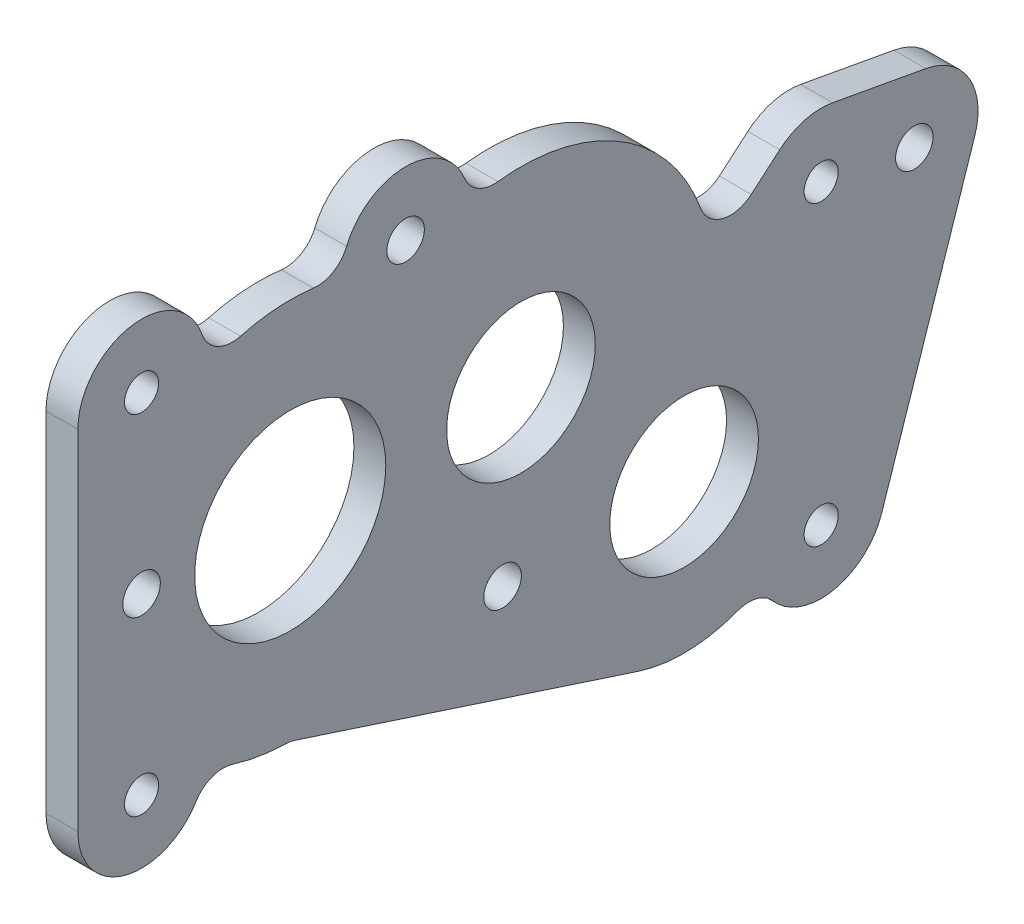
SolidWorks part; units mm, degrees
material "5052-H32"
ref_plane "Front Plane" through (0, 0, 0) normal (0, 0, 1) x (1, 0, 0)
ref_plane "Top Plane" through (0, 0, 0) normal (0, 1, 0) x (1, 0, 0)
ref_plane "Right Plane" through (0, 0, 0) normal (1, 0, 0) x (0, 0, -1)
sketch "Sketch1" plane through (0, 0, 0) normal (1, 0, 0) x (0, 0, -1)
  line L1 (0, 0) -> (146.05, 0)
  line L2 (0, 0) -> (0, 101.6)
  line L3 (0, 101.6) -> (146.05, 101.6)
  line L4 (146.05, 0) -> (146.05, 101.6)
  dimension "D1" = 146.05
  dimension "D2" = 101.6
extrude "Boss-Extrude2" add sketch "Sketch1" along normal blind 4.7625
sketch "Sketch2" plane through (4.7625, 0, 0) normal (1, 0, 0) x (0, 0, -1)
  circle A1 centre (66.2432, 57.15) radius 11.1125
  circle A7 centre (66.2432, 57.15) radius 11.1125
  circle A8 centre (31.75, 57.15) radius 11.1125
  circle A9 centre (31.75, 57.15) radius 11.1125
  circle A10 centre (90.6336, 32.7596) radius 14.2875
  circle A11 centre (90.6336, 32.7596) radius 14.2875
  dimension "D1" = 0
  dimension "D2" = 0
  dimension "D3" = 0
extrude "Cut-Extrude1" cut sketch "Sketch2" against normal through all
hole_wizard "#10 Clearance Hole1" positions "Sketch5" profile "Sketch6" hole size "#10" standard "ANSI Inch" end condition through all
sketch "Sketch5" plane through (4.7625, 0, 0) normal (1, 0, 0) x (0, 0, -1)
  circle A1 centre (111.125, 61.3346) radius 2.5527 construction
  circle A2 centre (9.525, 84.8296) radius 2.5527 construction
  circle A3 centre (9.525, 32.7596) radius 2.5527 construction
  circle A5 centre (111.125, 61.3346) radius 2.5527
  circle A6 centre (9.525, 84.8296) radius 2.5527
  circle A7 centre (9.525, 32.7596) radius 2.5527
  circle A8 centre (111.125, 16.8846) radius 2.5527 construction
  circle A9 centre (111.125, 16.8846) radius 2.5527
  point P423 (9.525, 84.8296)
  point P426 (111.125, 61.3346)
  point P432 (9.525, 32.7596)
  point P469 (111.125, 16.8846)
sketch "Sketch6" plane through (4.7625, 84.8296, -9.525) normal (0, 1, 0) x (0, 0, -1)
  line L0 (0, 0) -> (0, 4.7625)
  line L1 (0, 4.7625) -> (2.5527, 4.7625)
  line L2 (2.5527, 4.7625) -> (2.5527, 0)
  line L5 (2.5527, 0) -> (0, 0)
  line L11 (0, -6.35) -> (0, 107.95) construction
  dimension "Thru Hole Dia." = 5.1054
  dimension "Thru Hole Depth" = 4.7625
hole_wizard "#10 Clearance Hole2" positions "Sketch12" profile "Sketch13" hole size "#10" standard "ANSI Inch" end condition through all
sketch "Sketch12" plane through (4.7625, 0, 0) normal (1, 0, 0) x (0, 0, -1)
  line L0 (48.9966, 84.8296) -> (9.525, 84.8296) construction
  line L1 (9.525, 84.8296) -> (9.525, 32.7596) construction
  line L2 (9.525, 32.7596) -> (63.5, 32.7596) construction
  line L4 (9.525, 58.7946) -> (125.057, 58.7946) construction
  line L5 (66.2432, 57.15) -> (31.75, 57.15) construction
  point P0 (9.525, 58.7946)
  point P2 (48.9966, 84.8296)
  point P4 (125.057, 58.7946)
  point P6 (63.5, 32.7596)
  point P29 (48.9966, 57.15)
  point P30 (0, 0)
  point P31 (0, 0)
  dimension "D1" = 115.532
  dimension "D2" = 53.975
sketch "Sketch13" plane through (4.7625, 58.7946, -9.525) normal (0, 1, 0) x (0, 0, -1)
  line L0 (0, 0) -> (0, 4.7625)
  line L1 (0, 4.7625) -> (2.8067, 4.7625)
  line L2 (2.8067, 4.7625) -> (2.8067, 0)
  line L5 (2.8067, 0) -> (0, 0)
  line L11 (0, -6.35) -> (0, 107.95) construction
  dimension "Thru Hole Dia." = 5.6134
  dimension "Thru Hole Depth" = 4.7625
sketch "Sketch7" plane through (4.7625, 0, 0) normal (1, 0, 0) x (0, 0, -1)
  line L0 (9.525, 32.7596) -> (31.75, 57.15) construction
  line L1 (31.75, 57.15) -> (9.525, 84.8296) construction
  line L2 (31.75, 57.15) -> (66.2432, 57.15) construction
  line L3 (66.2432, 57.15) -> (90.6336, 32.7596) construction
  line L4 (90.6336, 32.7596) -> (111.125, 16.8846) construction
  line L5 (90.6336, 32.7596) -> (111.125, 61.3346) construction
  line L6 (111.125, 61.3346) -> (66.2432, 57.15) construction
  line L7 (94.6948, 59.8027) -> (104.9286, 68.5686)
  line L11 (31.75, 28.575) -> (83.7467, 11.6286)
  line L12 (0, 101.6) -> (146.05, 101.6)
  line L13 (0, 101.6) -> (0, 0)
  line L14 (0, 0) -> (146.05, 0)
  line L15 (146.05, 101.6) -> (146.05, 0)
  line L16 (0, 101.6) -> (0, 0) construction
  line L17 (112.8334, 70.7052) -> (126.7653, 68.1652)
  line L18 (134.0956, 55.7899) -> (120.1637, 13.8799)
  arc A0 (39.4731, 84.6615) -> (18.9777, 31.5883) centre (31.75, 57.15) ccw construction
  arc A1 (48.9966, 79.9334) -> (58.5201, 84.6615) centre (66.2432, 57.15) ccw construction
  arc A2 (103.5854, 50.8207) -> (111.9221, 26.3762) centre (90.6336, 32.7596) ccw construction
  arc A3 (111.9221, 26.3762) -> (120.1637, 13.8799) centre (111.125, 16.8846) ccw construction
  arc A4 (112.8334, 70.7052) -> (105.5742, 53.5942) centre (111.125, 61.3346) ccw construction
  arc A5 (15.9404, 39.8001) -> (18.9777, 31.5883) centre (9.525, 32.7596) ccw construction
  circle A6 centre (9.525, 84.8296) radius 9.525 construction
  arc A7 (104.9286, 68.5686) -> (112.8334, 70.7052) centre (111.125, 61.3346) cw
  arc A9 (120.1637, 13.8799) -> (102.1336, 13.7412) centre (111.125, 16.8846) cw
  arc A12 (31.75, 28.575) -> (18.9777, 31.5883) centre (31.75, 57.15) cw
  arc A13 (18.9777, 31.5883) -> (0, 32.7596) centre (9.525, 32.7596) cw
  arc A15 (0, 84.8296) -> (18.7894, 82.6167) centre (9.525, 84.8296) cw
  arc A16 (18.7894, 82.6167) -> (39.4731, 84.6615) centre (31.75, 57.15) cw
  arc A17 (58.5201, 84.6615) -> (94.6948, 59.8027) centre (66.2432, 57.15) cw
  arc A18 (39.4731, 84.6615) -> (58.5201, 84.6615) centre (48.9966, 84.8296) cw
  circle A19 centre (48.9966, 84.8296) radius 2.8067 construction
  arc A20 (18.9777, 31.5883) -> (48.9966, 79.9334) centre (31.75, 57.15) ccw construction
  arc A21 (83.7467, 11.6286) -> (102.1965, 13.7794) centre (90.6336, 32.7596) ccw
  arc A22 (134.0956, 55.7899) -> (126.7653, 68.1652) centre (125.057, 58.7946) ccw
  point P22 (108.1143, 70.7052)
  point P24 (94.6948, 59.8027)
  point P33 (134.4389, 57.15)
  line M17 (0, 101.6) -> (0, 0)
  line M18 (0, 0) -> (146.05, 0)
  line M19 (146.05, 0) -> (146.05, 101.6)
  line M20 (146.05, 101.6) -> (0, 101.6)
  dimension "D1" = 19.05
  dimension "D2" = 19.05
  dimension "D3" = 57.15
  dimension "D4" = 57.15
  dimension "D5" = 44.45
  dimension "D6" = 19.05
  dimension "D7" = 19.05
  dimension "D12" = 9.525
  dimension "D8" = 9.525
extrude "Cut-Extrude2" cut sketch "Sketch7" against normal through all contours A22 L18 A9 A21 L11 A12 A13 L13 A15 A16 A18 A17 L7 A7 L17 M18 M19 M20 M17
fillet "Fillet1" radius 4.7625 7 edges at (2.3813, 59.8027, -94.6948) (2.3813, 82.6167, -18.7894) (2.3813, 28.575, -31.75) (2.3813, 31.5883, -18.9777) (2.3813, 13.7412, -102.1336) (2.3813, 84.6615, -58.5201) (2.3813, 84.6615, -39.4731)
sketch "Sketch8" plane through (4.7625, 0, 0) normal (1, 0, 0) x (0, 0, -1)
  circle A0 centre (31.75, 57.15) radius 14.2875
  dimension "D1" = 28.575
extrude "Cut-Extrude3" cut sketch "Sketch8" against normal through all
sketch "Sketch9" plane through (4.7625, 0, 0) normal (1, 0, 0) x (0, 0, -1)
  circle A0 centre (90.6336, 32.7596) radius 11.1125
  circle A1 centre (90.6336, 32.7596) radius 14.2875 construction
  circle A2 centre (90.6336, 32.7596) radius 14.2875
  dimension "D1" = 22.225
extrude "Boss-Extrude3" add sketch "Sketch9" against normal up to surface (4.7625 mm away) up to face at (0, 57.15, -46.0375)
